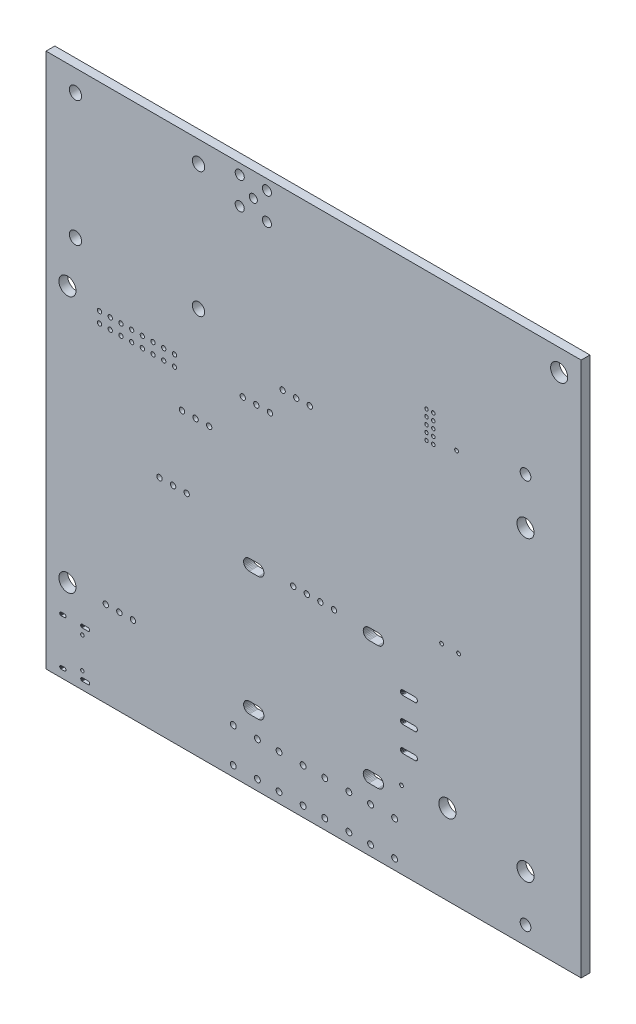
SolidWorks part; units mm, degrees
ref_plane "Přední rovina" through (0, 0, 0) normal (0, 0, 1) x (1, 0, 0)
ref_plane "Horní rovina" through (0, 0, 0) normal (0, 1, 0) x (1, 0, 0)
ref_plane "Pravá rovina" through (0, 0, 0) normal (1, 0, 0) x (0, 0, -1)
ref_plane "Rovina1" through (0, 0, 1.6472) normal (0, 0, 1) x (1, 0, 0)
sketch "Skica1" plane through (0, 0, 1.6472) normal (0, 0, 1) x (1, 0, 0)
  line L0 (40.2573, -63.262) -> (40.4165, -63.3925)
  line L1 (40.4165, -63.3925) -> (40.547, -63.5517)
  line L2 (40.547, -63.5517) -> (40.6441, -63.7332)
  line L3 (40.6441, -63.7332) -> (40.7038, -63.9302)
  line L4 (40.7038, -63.9302) -> (40.724, -64.135)
  line L5 (40.724, -64.135) -> (40.7038, -64.3398)
  line L6 (40.7038, -64.3398) -> (40.6441, -64.5368)
  line L7 (40.6441, -64.5368) -> (40.547, -64.7183)
  line L8 (40.547, -64.7183) -> (40.4165, -64.8775)
  line L9 (40.4165, -64.8775) -> (40.2573, -65.008)
  line L10 (40.2573, -65.008) -> (40.0758, -65.1051)
  line L11 (40.0758, -65.1051) -> (39.8788, -65.1648)
  line L12 (39.8788, -65.1648) -> (39.674, -65.185)
  line L13 (39.674, -65.185) -> (37.974, -65.185)
  line L14 (37.974, -65.185) -> (37.7692, -65.1648)
  line L15 (37.7692, -65.1648) -> (37.5722, -65.1051)
  line L16 (37.5722, -65.1051) -> (37.3907, -65.008)
  line L17 (37.3907, -65.008) -> (37.2315, -64.8775)
  line L18 (37.2315, -64.8775) -> (37.101, -64.7183)
  line L19 (37.101, -64.7183) -> (37.0039, -64.5368)
  line L20 (37.0039, -64.5368) -> (36.9442, -64.3398)
  line L21 (36.9442, -64.3398) -> (36.924, -64.135)
  line L22 (36.924, -64.135) -> (36.9442, -63.9302)
  line L23 (36.9442, -63.9302) -> (37.0039, -63.7332)
  line L24 (37.0039, -63.7332) -> (37.101, -63.5517)
  line L25 (37.101, -63.5517) -> (37.2315, -63.3925)
  line L26 (37.2315, -63.3925) -> (37.3907, -63.262)
  line L27 (37.3907, -63.262) -> (37.5722, -63.1649)
  line L28 (37.5722, -63.1649) -> (37.7692, -63.1052)
  line L29 (37.7692, -63.1052) -> (37.974, -63.085)
  line L30 (37.974, -63.085) -> (39.674, -63.085)
  line L31 (39.674, -63.085) -> (39.8788, -63.1052)
  line L32 (39.8788, -63.1052) -> (40.0758, -63.1649)
  line L33 (40.0758, -63.1649) -> (40.2573, -63.262)
  line L34 (3.6804, -89.4792) -> (3.7295, -89.5779)
  line L35 (3.7295, -89.5779) -> (3.7397, -89.6877)
  line L36 (3.7397, -89.6877) -> (3.7095, -89.7937)
  line L37 (3.7095, -89.7937) -> (3.6431, -89.8817)
  line L38 (3.6431, -89.8817) -> (3.5494, -89.9397)
  line L39 (3.5494, -89.9397) -> (3.441, -89.96)
  line L40 (3.441, -89.96) -> (2.841, -89.96)
  line L41 (2.841, -89.96) -> (2.7859, -89.9549)
  line L42 (2.7859, -89.9549) -> (2.6831, -89.9151)
  line L43 (2.6831, -89.9151) -> (2.6016, -89.8408)
  line L44 (2.6016, -89.8408) -> (2.5525, -89.7421)
  line L45 (2.5525, -89.7421) -> (2.5423, -89.6323)
  line L46 (2.5423, -89.6323) -> (2.5725, -89.5263)
  line L47 (2.5725, -89.5263) -> (2.6389, -89.4383)
  line L48 (2.6389, -89.4383) -> (2.7326, -89.3803)
  line L49 (2.7326, -89.3803) -> (2.841, -89.36)
  line L50 (2.841, -89.36) -> (3.441, -89.36)
  line L51 (3.441, -89.36) -> (3.4961, -89.3651)
  line L52 (3.4961, -89.3651) -> (3.5989, -89.4049)
  line L53 (3.5989, -89.4049) -> (3.6804, -89.4792)
  line L54 (8.1104, -89.4792) -> (8.1595, -89.5779)
  line L55 (8.1595, -89.5779) -> (8.1697, -89.6877)
  line L56 (8.1697, -89.6877) -> (8.1395, -89.7937)
  line L57 (8.1395, -89.7937) -> (8.0731, -89.8817)
  line L58 (8.0731, -89.8817) -> (7.9794, -89.9397)
  line L59 (7.9794, -89.9397) -> (7.871, -89.96)
  line L60 (7.871, -89.96) -> (6.771, -89.96)
  line L61 (6.771, -89.96) -> (6.7159, -89.9549)
  line L62 (6.7159, -89.9549) -> (6.6131, -89.9151)
  line L63 (6.6131, -89.9151) -> (6.5316, -89.8408)
  line L64 (6.5316, -89.8408) -> (6.4825, -89.7421)
  line L65 (6.4825, -89.7421) -> (6.4723, -89.6323)
  line L66 (6.4723, -89.6323) -> (6.5025, -89.5263)
  line L67 (6.5025, -89.5263) -> (6.5689, -89.4383)
  line L68 (6.5689, -89.4383) -> (6.6626, -89.3803)
  line L69 (6.6626, -89.3803) -> (6.771, -89.36)
  line L70 (6.771, -89.36) -> (7.871, -89.36)
  line L71 (7.871, -89.36) -> (7.9261, -89.3651)
  line L72 (7.9261, -89.3651) -> (8.0289, -89.4049)
  line L73 (8.0289, -89.4049) -> (8.1104, -89.4792)
  line L74 (3.6804, -98.1192) -> (3.7295, -98.2179)
  line L75 (3.7295, -98.2179) -> (3.7397, -98.3277)
  line L76 (3.7397, -98.3277) -> (3.7095, -98.4337)
  line L77 (3.7095, -98.4337) -> (3.6431, -98.5217)
  line L78 (3.6431, -98.5217) -> (3.5494, -98.5797)
  line L79 (3.5494, -98.5797) -> (3.441, -98.6)
  line L80 (3.441, -98.6) -> (2.841, -98.6)
  line L81 (2.841, -98.6) -> (2.7859, -98.5949)
  line L82 (2.7859, -98.5949) -> (2.6831, -98.5551)
  line L83 (2.6831, -98.5551) -> (2.6016, -98.4808)
  line L84 (2.6016, -98.4808) -> (2.5525, -98.3821)
  line L85 (2.5525, -98.3821) -> (2.5423, -98.2723)
  line L86 (2.5423, -98.2723) -> (2.5725, -98.1663)
  line L87 (2.5725, -98.1663) -> (2.6389, -98.0783)
  line L88 (2.6389, -98.0783) -> (2.7326, -98.0203)
  line L89 (2.7326, -98.0203) -> (2.841, -98)
  line L90 (2.841, -98) -> (3.441, -98)
  line L91 (3.441, -98) -> (3.4961, -98.0051)
  line L92 (3.4961, -98.0051) -> (3.5989, -98.0449)
  line L93 (3.5989, -98.0449) -> (3.6804, -98.1192)
  line L94 (8.1104, -98.1192) -> (8.1595, -98.2179)
  line L95 (8.1595, -98.2179) -> (8.1697, -98.3277)
  line L96 (8.1697, -98.3277) -> (8.1395, -98.4337)
  line L97 (8.1395, -98.4337) -> (8.0731, -98.5217)
  line L98 (8.0731, -98.5217) -> (7.9794, -98.5797)
  line L99 (7.9794, -98.5797) -> (7.871, -98.6)
  line L100 (7.871, -98.6) -> (6.771, -98.6)
  line L101 (6.771, -98.6) -> (6.7159, -98.5949)
  line L102 (6.7159, -98.5949) -> (6.6131, -98.5551)
  line L103 (6.6131, -98.5551) -> (6.5316, -98.4808)
  line L104 (6.5316, -98.4808) -> (6.4825, -98.3821)
  line L105 (6.4825, -98.3821) -> (6.4723, -98.2723)
  line L106 (6.4723, -98.2723) -> (6.5025, -98.1663)
  line L107 (6.5025, -98.1663) -> (6.5689, -98.0783)
  line L108 (6.5689, -98.0783) -> (6.6626, -98.0203)
  line L109 (6.6626, -98.0203) -> (6.771, -98)
  line L110 (6.771, -98) -> (7.871, -98)
  line L111 (7.871, -98) -> (7.9261, -98.0051)
  line L112 (7.9261, -98.0051) -> (8.0289, -98.0449)
  line L113 (8.0289, -98.0449) -> (8.1104, -98.1192)
  line L114 (40.2573, -86.376) -> (40.4165, -86.5065)
  line L115 (40.4165, -86.5065) -> (40.547, -86.6657)
  line L116 (40.547, -86.6657) -> (40.6441, -86.8472)
  line L117 (40.6441, -86.8472) -> (40.7038, -87.0442)
  line L118 (40.7038, -87.0442) -> (40.724, -87.249)
  line L119 (40.724, -87.249) -> (40.7038, -87.4538)
  line L120 (40.7038, -87.4538) -> (40.6441, -87.6508)
  line L121 (40.6441, -87.6508) -> (40.547, -87.8323)
  line L122 (40.547, -87.8323) -> (40.4165, -87.9915)
  line L123 (40.4165, -87.9915) -> (40.2573, -88.122)
  line L124 (40.2573, -88.122) -> (40.0758, -88.2191)
  line L125 (40.0758, -88.2191) -> (39.8788, -88.2788)
  line L126 (39.8788, -88.2788) -> (39.674, -88.299)
  line L127 (39.674, -88.299) -> (37.974, -88.299)
  line L128 (37.974, -88.299) -> (37.7692, -88.2788)
  line L129 (37.7692, -88.2788) -> (37.5722, -88.2191)
  line L130 (37.5722, -88.2191) -> (37.3907, -88.122)
  line L131 (37.3907, -88.122) -> (37.2315, -87.9915)
  line L132 (37.2315, -87.9915) -> (37.101, -87.8323)
  line L133 (37.101, -87.8323) -> (37.0039, -87.6508)
  line L134 (37.0039, -87.6508) -> (36.9442, -87.4538)
  line L135 (36.9442, -87.4538) -> (36.924, -87.249)
  line L136 (36.924, -87.249) -> (36.9442, -87.0442)
  line L137 (36.9442, -87.0442) -> (37.0039, -86.8472)
  line L138 (37.0039, -86.8472) -> (37.101, -86.6657)
  line L139 (37.101, -86.6657) -> (37.2315, -86.5065)
  line L140 (37.2315, -86.5065) -> (37.3907, -86.376)
  line L141 (37.3907, -86.376) -> (37.5722, -86.2789)
  line L142 (37.5722, -86.2789) -> (37.7692, -86.2192)
  line L143 (37.7692, -86.2192) -> (37.974, -86.199)
  line L144 (37.974, -86.199) -> (39.674, -86.199)
  line L145 (39.674, -86.199) -> (39.8788, -86.2192)
  line L146 (39.8788, -86.2192) -> (40.0758, -86.2789)
  line L147 (40.0758, -86.2789) -> (40.2573, -86.376)
  line L148 (62.6093, -63.262) -> (62.7685, -63.3925)
  line L149 (62.7685, -63.3925) -> (62.899, -63.5517)
  line L150 (62.899, -63.5517) -> (62.9961, -63.7332)
  line L151 (62.9961, -63.7332) -> (63.0558, -63.9302)
  line L152 (63.0558, -63.9302) -> (63.076, -64.135)
  line L153 (63.076, -64.135) -> (63.0558, -64.3398)
  line L154 (63.0558, -64.3398) -> (62.9961, -64.5368)
  line L155 (62.9961, -64.5368) -> (62.899, -64.7183)
  line L156 (62.899, -64.7183) -> (62.7685, -64.8775)
  line L157 (62.7685, -64.8775) -> (62.6093, -65.008)
  line L158 (62.6093, -65.008) -> (62.4278, -65.1051)
  line L159 (62.4278, -65.1051) -> (62.2308, -65.1648)
  line L160 (62.2308, -65.1648) -> (62.026, -65.185)
  line L161 (62.026, -65.185) -> (60.326, -65.185)
  line L162 (60.326, -65.185) -> (60.1212, -65.1648)
  line L163 (60.1212, -65.1648) -> (59.9242, -65.1051)
  line L164 (59.9242, -65.1051) -> (59.7427, -65.008)
  line L165 (59.7427, -65.008) -> (59.5835, -64.8775)
  line L166 (59.5835, -64.8775) -> (59.453, -64.7183)
  line L167 (59.453, -64.7183) -> (59.3559, -64.5368)
  line L168 (59.3559, -64.5368) -> (59.2962, -64.3398)
  line L169 (59.2962, -64.3398) -> (59.276, -64.135)
  line L170 (59.276, -64.135) -> (59.2962, -63.9302)
  line L171 (59.2962, -63.9302) -> (59.3559, -63.7332)
  line L172 (59.3559, -63.7332) -> (59.453, -63.5517)
  line L173 (59.453, -63.5517) -> (59.5835, -63.3925)
  line L174 (59.5835, -63.3925) -> (59.7427, -63.262)
  line L175 (59.7427, -63.262) -> (59.9242, -63.1649)
  line L176 (59.9242, -63.1649) -> (60.1212, -63.1052)
  line L177 (60.1212, -63.1052) -> (60.326, -63.085)
  line L178 (60.326, -63.085) -> (62.026, -63.085)
  line L179 (62.026, -63.085) -> (62.2308, -63.1052)
  line L180 (62.2308, -63.1052) -> (62.4278, -63.1649)
  line L181 (62.4278, -63.1649) -> (62.6093, -63.262)
  line L182 (69.2741, -70.1551) -> (69.3577, -70.26)
  line L183 (69.3577, -70.26) -> (69.4067, -70.3849)
  line L184 (69.4067, -70.3849) -> (69.4167, -70.5186)
  line L185 (69.4167, -70.5186) -> (69.3869, -70.6494)
  line L186 (69.3869, -70.6494) -> (69.3198, -70.7656)
  line L187 (69.3198, -70.7656) -> (69.2215, -70.8568)
  line L188 (69.2215, -70.8568) -> (69.1006, -70.915)
  line L189 (69.1006, -70.915) -> (68.968, -70.935)
  line L190 (68.968, -70.935) -> (66.668, -70.935)
  line L191 (66.668, -70.935) -> (66.6009, -70.93)
  line L192 (66.6009, -70.93) -> (66.4728, -70.8904)
  line L193 (66.4728, -70.8904) -> (66.3619, -70.8149)
  line L194 (66.3619, -70.8149) -> (66.2783, -70.71)
  line L195 (66.2783, -70.71) -> (66.2293, -70.5851)
  line L196 (66.2293, -70.5851) -> (66.2193, -70.4514)
  line L197 (66.2193, -70.4514) -> (66.2491, -70.3206)
  line L198 (66.2491, -70.3206) -> (66.3162, -70.2044)
  line L199 (66.3162, -70.2044) -> (66.4145, -70.1132)
  line L200 (66.4145, -70.1132) -> (66.5354, -70.055)
  line L201 (66.5354, -70.055) -> (66.668, -70.035)
  line L202 (66.668, -70.035) -> (68.968, -70.035)
  line L203 (68.968, -70.035) -> (69.0351, -70.04)
  line L204 (69.0351, -70.04) -> (69.1632, -70.0796)
  line L205 (69.1632, -70.0796) -> (69.2741, -70.1551)
  line L206 (69.2741, -74.8541) -> (69.3577, -74.959)
  line L207 (69.3577, -74.959) -> (69.4067, -75.0839)
  line L208 (69.4067, -75.0839) -> (69.4167, -75.2176)
  line L209 (69.4167, -75.2176) -> (69.3869, -75.3484)
  line L210 (69.3869, -75.3484) -> (69.3198, -75.4646)
  line L211 (69.3198, -75.4646) -> (69.2215, -75.5558)
  line L212 (69.2215, -75.5558) -> (69.1006, -75.614)
  line L213 (69.1006, -75.614) -> (68.968, -75.634)
  line L214 (68.968, -75.634) -> (66.668, -75.634)
  line L215 (66.668, -75.634) -> (66.6009, -75.629)
  line L216 (66.6009, -75.629) -> (66.4728, -75.5894)
  line L217 (66.4728, -75.5894) -> (66.3619, -75.5139)
  line L218 (66.3619, -75.5139) -> (66.2783, -75.409)
  line L219 (66.2783, -75.409) -> (66.2293, -75.2841)
  line L220 (66.2293, -75.2841) -> (66.2193, -75.1504)
  line L221 (66.2193, -75.1504) -> (66.2491, -75.0196)
  line L222 (66.2491, -75.0196) -> (66.3162, -74.9034)
  line L223 (66.3162, -74.9034) -> (66.4145, -74.8122)
  line L224 (66.4145, -74.8122) -> (66.5354, -74.754)
  line L225 (66.5354, -74.754) -> (66.668, -74.734)
  line L226 (66.668, -74.734) -> (68.968, -74.734)
  line L227 (68.968, -74.734) -> (69.0351, -74.739)
  line L228 (69.0351, -74.739) -> (69.1632, -74.7786)
  line L229 (69.1632, -74.7786) -> (69.2741, -74.8541)
  line L230 (69.2741, -79.5531) -> (69.3577, -79.658)
  line L231 (69.3577, -79.658) -> (69.4067, -79.7829)
  line L232 (69.4067, -79.7829) -> (69.4167, -79.9166)
  line L233 (69.4167, -79.9166) -> (69.3869, -80.0474)
  line L234 (69.3869, -80.0474) -> (69.3198, -80.1636)
  line L235 (69.3198, -80.1636) -> (69.2215, -80.2548)
  line L236 (69.2215, -80.2548) -> (69.1006, -80.313)
  line L237 (69.1006, -80.313) -> (68.968, -80.333)
  line L238 (68.968, -80.333) -> (66.668, -80.333)
  line L239 (66.668, -80.333) -> (66.6009, -80.328)
  line L240 (66.6009, -80.328) -> (66.4728, -80.2884)
  line L241 (66.4728, -80.2884) -> (66.3619, -80.2129)
  line L242 (66.3619, -80.2129) -> (66.2783, -80.108)
  line L243 (66.2783, -80.108) -> (66.2293, -79.9831)
  line L244 (66.2293, -79.9831) -> (66.2193, -79.8494)
  line L245 (66.2193, -79.8494) -> (66.2491, -79.7186)
  line L246 (66.2491, -79.7186) -> (66.3162, -79.6024)
  line L247 (66.3162, -79.6024) -> (66.4145, -79.5112)
  line L248 (66.4145, -79.5112) -> (66.5354, -79.453)
  line L249 (66.5354, -79.453) -> (66.668, -79.433)
  line L250 (66.668, -79.433) -> (68.968, -79.433)
  line L251 (68.968, -79.433) -> (69.0351, -79.438)
  line L252 (69.0351, -79.438) -> (69.1632, -79.4776)
  line L253 (69.1632, -79.4776) -> (69.2741, -79.5531)
  line L254 (62.6093, -86.376) -> (62.7685, -86.5065)
  line L255 (62.7685, -86.5065) -> (62.899, -86.6657)
  line L256 (62.899, -86.6657) -> (62.9961, -86.8472)
  line L257 (62.9961, -86.8472) -> (63.0558, -87.0442)
  line L258 (63.0558, -87.0442) -> (63.076, -87.249)
  line L259 (63.076, -87.249) -> (63.0558, -87.4538)
  line L260 (63.0558, -87.4538) -> (62.9961, -87.6508)
  line L261 (62.9961, -87.6508) -> (62.899, -87.8323)
  line L262 (62.899, -87.8323) -> (62.7685, -87.9915)
  line L263 (62.7685, -87.9915) -> (62.6093, -88.122)
  line L264 (62.6093, -88.122) -> (62.4278, -88.2191)
  line L265 (62.4278, -88.2191) -> (62.2308, -88.2788)
  line L266 (62.2308, -88.2788) -> (62.026, -88.299)
  line L267 (62.026, -88.299) -> (60.326, -88.299)
  line L268 (60.326, -88.299) -> (60.1212, -88.2788)
  line L269 (60.1212, -88.2788) -> (59.9242, -88.2191)
  line L270 (59.9242, -88.2191) -> (59.7427, -88.122)
  line L271 (59.7427, -88.122) -> (59.5835, -87.9915)
  line L272 (59.5835, -87.9915) -> (59.453, -87.8323)
  line L273 (59.453, -87.8323) -> (59.3559, -87.6508)
  line L274 (59.3559, -87.6508) -> (59.2962, -87.4538)
  line L275 (59.2962, -87.4538) -> (59.276, -87.249)
  line L276 (59.276, -87.249) -> (59.2962, -87.0442)
  line L277 (59.2962, -87.0442) -> (59.3559, -86.8472)
  line L278 (59.3559, -86.8472) -> (59.453, -86.6657)
  line L279 (59.453, -86.6657) -> (59.5835, -86.5065)
  line L280 (59.5835, -86.5065) -> (59.7427, -86.376)
  line L281 (59.7427, -86.376) -> (59.9242, -86.2789)
  line L282 (59.9242, -86.2789) -> (60.1212, -86.2192)
  line L283 (60.1212, -86.2192) -> (60.326, -86.199)
  line L284 (60.326, -86.199) -> (62.026, -86.199)
  line L285 (62.026, -86.199) -> (62.2308, -86.2192)
  line L286 (62.2308, -86.2192) -> (62.4278, -86.2789)
  line L287 (62.4278, -86.2789) -> (62.6093, -86.376)
  line L288 (100, 0) -> (0, 0)
  line L289 (0, 0) -> (0, -100)
  line L290 (0, -100) -> (100, -100)
  line L291 (100, -100) -> (100, 0)
  circle A0 centre (5.5, -4) radius 1.15
  circle A1 centre (28.5, -4) radius 1.15
  circle A2 centre (36.195, -1.92) radius 0.85
  circle A3 centre (36.195, -7) radius 0.85
  circle A4 centre (41.275, -1.92) radius 0.85
  circle A5 centre (38.735, -4.46) radius 0.75
  circle A6 centre (41.275, -7) radius 0.85
  circle A7 centre (5.5, -27.46) radius 1.15
  circle A8 centre (4, -36) radius 1.6
  circle A9 centre (10, -37.08) radius 0.4
  circle A10 centre (12, -37.08) radius 0.4
  circle A11 centre (14, -37.08) radius 0.4
  circle A12 centre (16, -37.08) radius 0.4
  circle A13 centre (18, -37.08) radius 0.4
  circle A14 centre (20, -37.08) radius 0.4
  circle A15 centre (22, -37.08) radius 0.4
  circle A16 centre (24, -37.08) radius 0.4
  circle A17 centre (10, -39.08) radius 0.4
  circle A18 centre (12, -39.08) radius 0.4
  circle A19 centre (14, -39.08) radius 0.4
  circle A20 centre (16, -39.08) radius 0.4
  circle A21 centre (18, -39.08) radius 0.4
  circle A22 centre (20, -39.08) radius 0.4
  circle A23 centre (22, -39.08) radius 0.4
  circle A24 centre (24, -39.08) radius 0.4
  circle A25 centre (25.415, -45.466) radius 0.5
  circle A26 centre (28.5, -27.46) radius 1.15
  circle A27 centre (36.766, -37.592) radius 0.5
  circle A28 centre (39.306, -37.592) radius 0.5
  circle A29 centre (41.846, -37.592) radius 0.5
  circle A30 centre (44.211, -32.766) radius 0.5
  circle A31 centre (46.751, -32.766) radius 0.5
  circle A32 centre (49.291, -32.766) radius 0.5
  circle A33 centre (27.955, -45.466) radius 0.5
  circle A34 centre (30.495, -45.466) radius 0.5
  circle A35 centre (71.1, -22.37) radius 0.325
  circle A36 centre (72.37, -22.37) radius 0.325
  circle A37 centre (71.1, -23.64) radius 0.325
  circle A38 centre (72.37, -23.64) radius 0.325
  circle A39 centre (71.1, -24.91) radius 0.325
  circle A40 centre (72.37, -24.91) radius 0.325
  circle A41 centre (95.885, -4.064) radius 1.6
  circle A42 centre (89.6, -23.7) radius 1
  circle A43 centre (71.1, -26.18) radius 0.325
  circle A44 centre (72.37, -26.18) radius 0.325
  circle A45 centre (71.1, -27.45) radius 0.325
  circle A46 centre (72.37, -27.45) radius 0.325
  circle A47 centre (76.708, -26.289) radius 0.35
  circle A48 centre (89.6, -32.345) radius 1.6
  circle A49 centre (21.209, -58.42) radius 0.5
  circle A50 centre (23.749, -58.42) radius 0.5
  circle A51 centre (26.289, -58.42) radius 0.5
  circle A52 centre (46.19, -63.5) radius 0.5
  circle A53 centre (48.73, -63.5) radius 0.5
  circle A54 centre (4, -84) radius 1.6
  circle A55 centre (11.161, -83.947) radius 0.5
  circle A56 centre (13.701, -83.947) radius 0.5
  circle A57 centre (16.241, -83.947) radius 0.5
  circle A58 centre (6.791, -91.09) radius 0.325
  circle A59 centre (6.791, -96.87) radius 0.325
  circle A60 centre (34.992, -91.58) radius 0.55
  circle A61 centre (34.992, -98.08) radius 0.55
  circle A62 centre (39.492, -91.58) radius 0.55
  circle A63 centre (43.542, -91.58) radius 0.55
  circle A64 centre (48.042, -91.58) radius 0.55
  circle A65 centre (39.492, -98.08) radius 0.55
  circle A66 centre (43.542, -98.08) radius 0.55
  circle A67 centre (48.042, -98.08) radius 0.55
  circle A68 centre (51.27, -63.5) radius 0.5
  circle A69 centre (53.81, -63.5) radius 0.5
  circle A70 centre (73.914, -58.928) radius 0.35
  circle A71 centre (77.089, -58.928) radius 0.35
  circle A72 centre (66.421, -85.598) radius 0.35
  circle A73 centre (52.092, -91.58) radius 0.55
  circle A74 centre (56.592, -91.58) radius 0.55
  circle A75 centre (60.642, -91.58) radius 0.55
  circle A76 centre (52.092, -98.08) radius 0.55
  circle A77 centre (56.592, -98.08) radius 0.55
  circle A78 centre (60.642, -98.08) radius 0.55
  circle A79 centre (65.142, -91.58) radius 0.55
  circle A80 centre (65.142, -98.08) radius 0.55
  circle A81 centre (75, -85) radius 1.6
  circle A82 centre (89.6, -87.955) radius 1.6
  circle A83 centre (89.6, -96.6) radius 1
  dimension "D2" = 72.9
  dimension "D1" = 3.4
extrude "Přidat vysunutím1" add sketch "Skica1" against normal blind 1.6472
